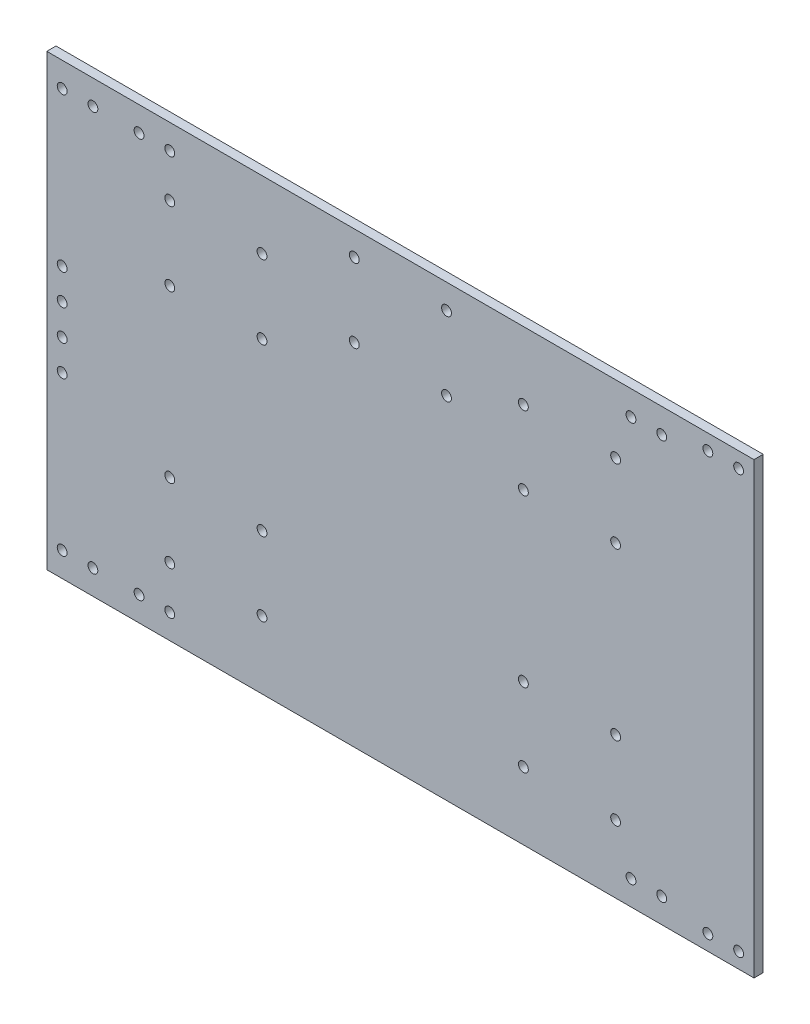
SolidWorks part; units mm, degrees
material "Thornel Mat VMA"
ref_plane "前视基准面" through (0, 0, 0) normal (0, 0, 1) x (1, 0, 0)
ref_plane "上视基准面" through (0, 0, 0) normal (0, 1, 0) x (1, 0, 0)
ref_plane "右视基准面" through (0, 0, 0) normal (1, 0, 0) x (0, 0, -1)
other "Configuration Table"
sketch "草图1" plane through (0, 0, 0) normal (0, 0, 1) x (1, 0, 0)
  line L0 (-133.3846, 27.6304) -> (96.6154, 27.6304) construction
  line L1 (-133.3846, 100.6304) -> (96.6154, 100.6304)
  line L2 (-133.3846, 100.6304) -> (-133.3846, -45.3696)
  line L3 (-133.3846, -45.3696) -> (96.6154, -45.3696)
  line L4 (96.6154, 100.6304) -> (96.6154, -45.3696)
  line L5 (-18.3846, 100.6304) -> (-18.3846, -45.3696) construction
  line L6 (96.6154, -40.3696) -> (81.6154, -40.3696) construction
  line L7 (81.6154, -40.3696) -> (81.6154, -45.3696) construction
  line L8 (-128.3846, 27.6304) -> (-128.3846, 7.8919) construction
  line L9 (21.6154, 0.6304) -> (51.6154, 0.6304) construction
  line L10 (21.6154, 0.6304) -> (21.6154, -23.3696) construction
  line L11 (21.6154, -23.3696) -> (51.6154, -23.3696) construction
  line L12 (51.6154, 0.6304) -> (51.6154, -23.3696) construction
  line L13 (-93.3846, 0.6304) -> (-63.3846, 0.6304) construction
  line L14 (-93.3846, 0.6304) -> (-93.3846, -23.3696) construction
  line L15 (-93.3846, -23.3696) -> (-63.3846, -23.3696) construction
  line L16 (-63.3846, 0.6304) -> (-63.3846, -23.3696) construction
  line L17 (-33.3846, 92.6304) -> (-3.3846, 92.6304) construction
  line L18 (-33.3846, 92.6304) -> (-33.3846, 68.6304) construction
  line L19 (-33.3846, 68.6304) -> (-3.3846, 68.6304) construction
  line L20 (-3.3846, 92.6304) -> (-3.3846, 68.6304) construction
  line L21 (-128.3846, 7.8919) -> (-133.3846, 7.8919) construction
  line L22 (66.6154, -45.3696) -> (66.6154, -37.3696) construction
  line L23 (66.6154, -37.3696) -> (56.6154, -37.3696) construction
  line L24 (56.6154, -37.3696) -> (56.6154, -45.3696) construction
  line L25 (-133.3846, -37.3696) -> (-118.3846, -37.3696) construction
  line L26 (-118.3846, -37.3696) -> (-118.3846, -45.3696) construction
  line L27 (36.6154, 0.6304) -> (36.6154, -71.6637) construction
  circle A8 centre (51.6154, 0.6304) radius 1.6
  circle A9 centre (51.6154, -23.3696) radius 1.6
  circle A10 centre (21.6154, -23.3696) radius 1.6
  circle A11 centre (21.6154, 0.6304) radius 1.6
  circle A12 centre (51.6154, 54.6304) radius 1.6
  circle A13 centre (51.6154, 78.6304) radius 1.6
  circle A14 centre (21.6154, 78.6304) radius 1.6
  circle A15 centre (21.6154, 54.6304) radius 1.6
  circle A16 centre (-63.3846, 0.6304) radius 1.6
  circle A17 centre (-63.3846, -23.3696) radius 1.6
  circle A18 centre (-93.3846, -23.3696) radius 1.6
  circle A19 centre (-93.3846, 0.6304) radius 1.6
  circle A20 centre (-63.3846, 54.6304) radius 1.6
  circle A21 centre (-63.3846, 78.6304) radius 1.6
  circle A22 centre (-93.3846, 78.6304) radius 1.6
  circle A23 centre (-93.3846, 54.6304) radius 1.6
  circle A32 centre (-3.3846, 92.6304) radius 1.6
  circle A33 centre (-3.3846, 68.6304) radius 1.6
  circle A34 centre (-33.3846, 68.6304) radius 1.6
  circle A35 centre (-33.3846, 92.6304) radius 1.6
  circle A36 centre (-128.3846, 22.6304) radius 1.6
  circle A37 centre (-128.3846, 12.6304) radius 1.6
  circle A38 centre (-128.3846, 42.6304) radius 1.6
  circle A39 centre (-128.3846, 32.6304) radius 1.6
  circle A40 centre (91.6154, -40.3696) radius 1.6
  circle A41 centre (81.6154, -40.3696) radius 1.6
  circle A42 centre (66.6154, -37.3696) radius 1.6
  circle A43 centre (56.6154, -37.3696) radius 1.6
  circle A44 centre (91.6154, 95.6304) radius 1.6
  circle A45 centre (81.6154, 95.6304) radius 1.6
  circle A46 centre (56.6154, 92.6304) radius 1.6
  circle A47 centre (66.6154, 92.6304) radius 1.6
  circle A50 centre (-103.3846, -37.3696) radius 1.6
  circle A51 centre (-93.3846, -37.3696) radius 1.6
  circle A54 centre (-93.3846, 92.6304) radius 1.6
  circle A55 centre (-103.3846, 92.6304) radius 1.6
  circle A56 centre (-118.3846, -37.3696) radius 1.6
  circle A57 centre (-128.3846, -37.3696) radius 1.6
  circle A58 centre (-118.3846, 92.6304) radius 1.6
  circle A59 centre (-128.3846, 92.6304) radius 1.6
  point P99 (-18.3846, 92.6304)
  dimension "D3" = 3.2
  dimension "D8" = 8
  dimension "D9" = 3.2
  dimension "D16" = 3.2
  dimension "D19" = 3.2
  dimension "D25" = 5
  dimension "D27" = 3.2
  dimension "D29" = 8
  dimension "D32" = 3.2
  dimension "D1" = 230
  dimension "D2" = 146
  dimension "D4" = 5
  dimension "D5" = 10
  dimension "D6" = 5
  dimension "D7" = 15
  dimension "D10" = 30
  dimension "D11" = 24
  dimension "D12" = 22
  dimension "D13" = 40
  dimension "D14" = 30
  dimension "D15" = 24
  dimension "D17" = 22
  dimension "D18" = 40
  dimension "D20" = 30
  dimension "D21" = 24
  dimension "D22" = 8
  dimension "D24" = 5
  dimension "D26" = 10
  dimension "D28" = 10
  dimension "D30" = 5
  dimension "D31" = 10
  dimension "D33" = 230
extrude "凸台-拉伸1" add sketch "草图1" along normal blind 3
sketch "草图2" plane through (0, 0, 3) normal (0, 0, 1) x (1, 0, 0)
  line L0 (-63.3846, 78.6304) -> (-93.3846, 78.6304)
  line L1 (21.6154, 78.6304) -> (51.6154, 78.6304)
  line L2 (36.6154, 78.6304) -> (-78.3846, 78.6304)
  line L3 (96.6154, 100.6304) -> (96.6154, -45.3696)
  dimension "D1" = 115
  dimension "D2" = 146
